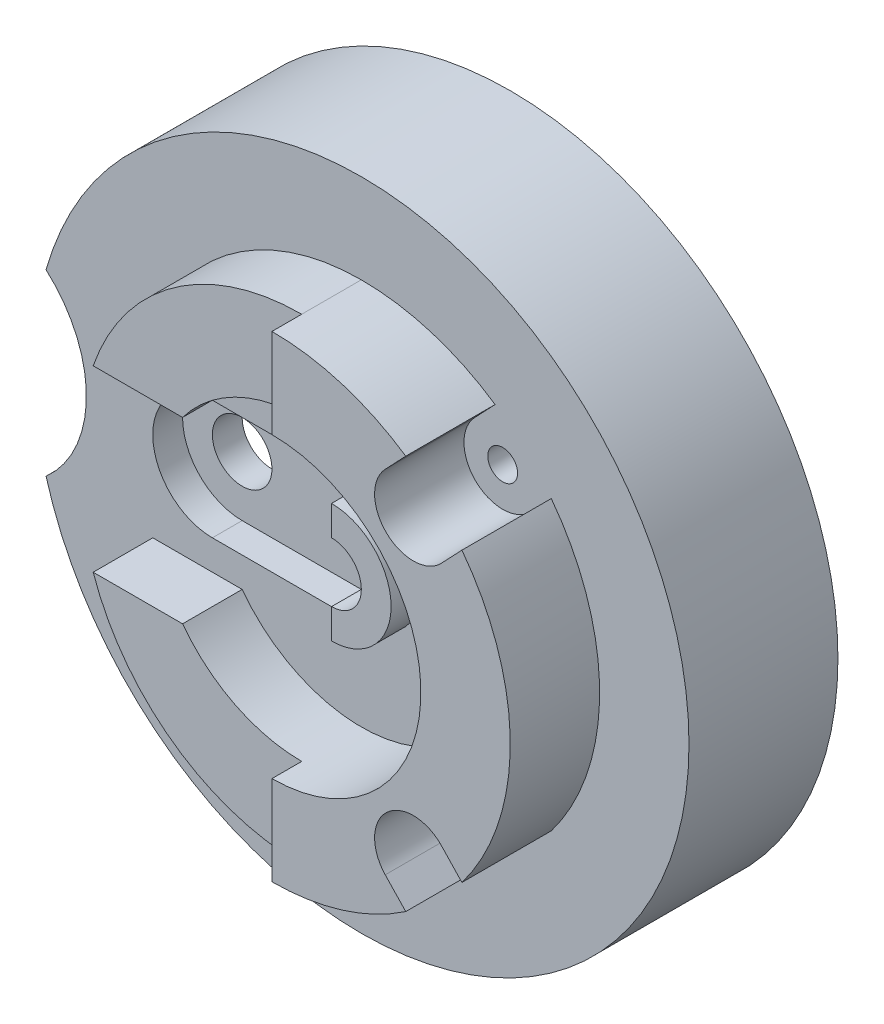
SolidWorks part; units mm, degrees
ref_plane "Front Plane" through (0, 0, 0) normal (0, 0, 1) x (1, 0, 0)
ref_plane "Top Plane" through (0, 0, 0) normal (0, 1, 0) x (1, 0, 0)
ref_plane "Right Plane" through (0, 0, 0) normal (1, 0, 0) x (0, 0, -1)
sketch "Sketch3" plane through (0, 0, 0) normal (0, 0, 1) x (1, 0, 0)
  circle A0 centre (0, 0) radius 55
  dimension "D1" = 110
extrude "Boss-Extrude2" add sketch "Sketch3" along normal blind 25
sketch "Sketch4" plane through (0, 0, 0) normal (0, 0, -1) x (-1, 0, 0)
  circle A0 centre (0, 0) radius 50
  dimension "D1" = 100
extrude "Cut-Extrude1" cut sketch "Sketch4" against normal blind 15
sketch "Sketch5" plane through (0, 0, 25) normal (0, 0, 1) x (1, 0, 0)
  arc A0 (-52.915, 15) -> (-52.915, -15) centre (-66.1438, 0) cw
  circle A1 centre (0, 0) radius 55 construction
  arc A2 (-52.915, -15) -> (-52.915, 15) centre (0, 0) cw
  dimension "D3" = 55
  dimension "D2" = 20
  dimension "D1" = 30
extrude "Cut-Extrude2" cut sketch "Sketch5" against normal blind 15
sketch "Sketch6" plane through (0, 0, 25) normal (0, 0, 1) x (1, 0, 0)
  line L0 (-35, 15) -> (-20, 15)
  line L1 (0, 40) -> (0, 25)
  arc A0 (-35, 15) -> (0, 40) centre (0, 3) cw
  arc A1 (-20, 15) -> (0, 25) centre (0, 0) cw
  dimension "D3" = 25
  dimension "D1" = 15
  dimension "D2" = 15
  dimension "D5" = 15
  dimension "D6" = 20
extrude "Boss-Extrude3" add sketch "Sketch6" along normal blind 10
sketch "Sketch7" plane through (0, 0, 25) normal (0, 0, 1) x (1, 0, 0)
  line L0 (0, 25) -> (0, 40)
  line L1 (0, -25) -> (0, -40)
  line L2 (-35, -15) -> (-20, -15)
  line L3 (-35, 15) -> (-20, 15) construction
  arc A0 (0, 25) -> (-20, 15) centre (0, 0) ccw construction
  arc A1 (-20, -15) -> (0, -25) centre (0, 0) ccw
  arc A2 (-35, -15) -> (0, -40) centre (0, -3) ccw
  arc A3 (0, 25) -> (-20, 15) centre (0, 0) ccw construction
  point P23 (-27.5, 15)
  dimension "D2" = 30
  dimension "D1" = 15
extrude "Boss-Extrude4" add sketch "Sketch7" along normal blind 10 contours L2 A2 L1 A1
sketch "Sketch8" plane through (0, 0, 25) normal (0, 0, 1) x (1, 0, 0)
  line L0 (0, -40) -> (0, -25)
  line L1 (0, 25) -> (0, 40)
  arc A0 (0, -40) -> (0, 40) centre (0, 0) ccw
  arc A1 (0, -25) -> (0, 25) centre (0, 0) ccw
  dimension "D1" = 25
  dimension "D2" = 40
extrude "Boss-Extrude5" add sketch "Sketch8" along normal blind 15
sketch "Sketch9" plane through (0, 0, 40) normal (0, 0, 1) x (1, 0, 0)
  line L0 (19.0146, -29.4748) -> (22.4567, -33.1013)
  line L1 (28.4435, -20.5252) -> (31.8856, -24.1517)
  line L2 (22.4567, 33.1013) -> (19.0146, 29.4748)
  line L3 (31.8856, 24.1517) -> (28.4435, 20.5252)
  arc A0 (0, -40) -> (0, 40) centre (0, 0) ccw construction
  arc A1 (19.0146, -29.4748) -> (28.4435, -20.5252) centre (23.729, -25) cw
  arc A2 (22.4567, -33.1013) -> (31.8856, -24.1517) centre (0, 0) ccw
  arc A4 (28.4435, 20.5252) -> (19.0146, 29.4748) centre (23.729, 25) cw
  arc A5 (31.8856, 24.1517) -> (22.4567, 33.1013) centre (0, 0) ccw
  dimension "D2" = 6.5
  dimension "D3" = 25
  dimension "D4" = 40
  dimension "D6" = 6.5
  dimension "D8" = 40
  dimension "D1" = 5
  dimension "D5" = 5
  dimension "D7" = 25
extrude "Cut-Extrude4" cut sketch "Sketch9" against normal blind 15
sketch "Sketch11" plane through (0, 0, 25) normal (0, 0, 1) x (1, 0, 0)
  circle A0 centre (23.729, -25) radius 2.5
  circle A1 centre (23.729, 25) radius 2.5
  point P0 (23.729, -25)
  point P4 (23.729, 25)
  dimension "D1" = 5
  dimension "D2" = 5
extrude "Cut-Extrude7" cut sketch "Sketch11" against normal blind 25
sketch "Sketch12" plane through (0, 0, 25) normal (0, 0, 1) x (1, 0, 0)
  circle A0 centre (15, 0) radius 2.5
  dimension "D1" = 5
  dimension "D2" = 15
extrude "Cut-Extrude9" cut sketch "Sketch12" against normal blind 10
sketch "Sketch13" plane through (0, 0, 25) normal (0, 0, 1) x (1, 0, 0)
  line L0 (-25, 0) -> (0, 0) construction
  line L1 (-25, 10) -> (0, 10)
  line L2 (-25, -10) -> (0, -10)
  arc A0 (-25, 10) -> (-25, -10) centre (-25, 0) ccw
  arc A1 (0, -10) -> (0, 10) centre (0, 0) ccw
  point P3 (-12.5, 0)
  dimension "D2" = 10
  dimension "D1" = 25
extrude "Cut-Extrude12" cut sketch "Sketch13" against normal blind 5
sketch "Sketch14" plane through (0, 0, 20) normal (0, 0, 1) x (1, 0, 0)
  circle A0 centre (-25, 0) radius 5
  circle A1 centre (0, 0) radius 5
  dimension "D1" = 10
  dimension "D2" = 10
  dimension "D3" = 25
extrude "Cut-Extrude13" cut sketch "Sketch14" against normal blind 10
sketch "Sketch15" plane through (0, 0, 20) normal (0, 0, 1) x (1, 0, 0)
  line L0 (0, 5) -> (0, 10)
  line L1 (0, -10) -> (0, -5)
  circle A0 centre (0, 0) radius 5 construction
  arc A1 (0, -10) -> (0, 10) centre (0, 0) ccw construction
  arc A2 (0, -5) -> (0, 5) centre (0, 0) ccw
  arc A3 (0, 10) -> (0, -10) centre (0, 0) cw
  dimension "D1" = 5
  dimension "D2" = 10
extrude "Boss-Extrude6" add sketch "Sketch15" along normal blind 10
